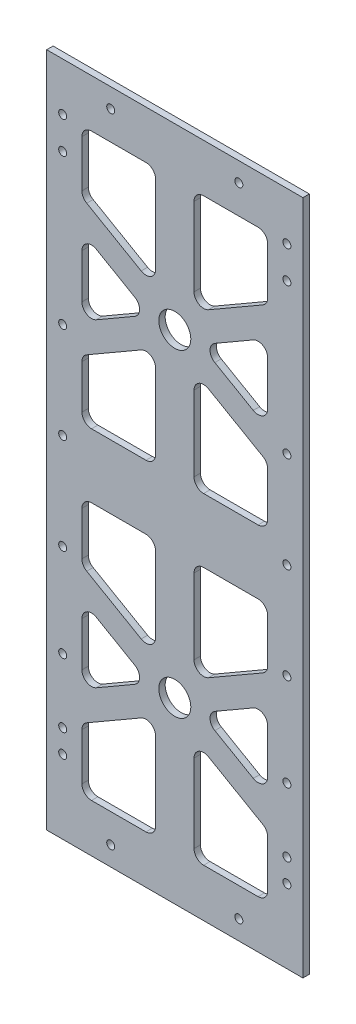
SolidWorks part; units mm, degrees
material "6061-T6 (SS)"
ref_plane "Front Plane" through (0, 0, 0) normal (0, 0, 1) x (1, 0, 0)
ref_plane "Top Plane" through (0, 0, 0) normal (0, 1, 0) x (1, 0, 0)
ref_plane "Right Plane" through (0, 0, 0) normal (1, 0, 0) x (0, 0, -1)
sketch "Sketch1" plane through (0, 0, 0) normal (0, 0, 1) x (1, 0, 0)
  line L1 (0, 0) -> (88, 0)
  line L2 (0, 0) -> (0, 211)
  line L3 (0, 211) -> (88, 211)
  line L4 (88, 0) -> (88, 211)
  dimension "D1" = 88
  dimension "D2" = 211
extrude "Boss-Extrude1" add sketch "Sketch1" along normal blind 2
sketch "Sketch2" plane through (0, 0, 2) normal (0, 0, 1) x (1, 0, 0)
  line L0 (0, 105.5) -> (88, 105.5) construction
  line L1 (0, 211) -> (0, 0) construction
  line L2 (88, 0) -> (88, 211) construction
  line L3 (44, 211) -> (44, 0) construction
  line L4 (88, 211) -> (0, 211) construction
  line L5 (0, 0) -> (88, 0) construction
  line L6 (0, 155.25) -> (88, 155.25) construction
  line L7 (0, 55.75) -> (88, 55.75) construction
  dimension "D1" = 55.75
  dimension "D2" = 55.75
sketch "Sketch3" plane through (0, 0, 2) normal (0, 0, 1) x (1, 0, 0)
  line L0 (0, 155.25) -> (88, 155.25) construction
  line L1 (38, 196) -> (38, 115.5)
  line L2 (0, 211) -> (0, 0) construction
  line L3 (15, 196) -> (73, 196)
  line L4 (15, 196) -> (15, 115.5)
  line L5 (15, 115.5) -> (73, 115.5)
  line L6 (73, 196) -> (73, 115.5)
  line L7 (88, 211) -> (0, 211) construction
  line L8 (88, 0) -> (88, 211) construction
  line L9 (0, 105.5) -> (88, 105.5) construction
  line L13 (73, 171.9932) -> (15, 138.5068) construction
  line L14 (15, 171.9932) -> (73, 138.5068) construction
  line L15 (73, 176.612) -> (15, 143.1256)
  line L16 (73, 167.3744) -> (15, 133.888)
  line L17 (15, 176.612) -> (73, 143.1256)
  line L18 (15, 167.3744) -> (73, 133.888)
  line L19 (50, 196) -> (50, 115.5)
  circle A0 centre (44, 155.25) radius 5
  dimension "D1" = 10
  dimension "D3" = 15
  dimension "D4" = 15
  dimension "D5" = 15
  dimension "D6" = 10
  dimension "D9" = 30
  dimension "D10" = 30
  dimension "D11" = 8
  dimension "D12" = 4
  dimension "D13" = 4
  dimension "D14" = 8
ref_plane "Plane1" through (0, 105.5, 0) normal (0, 1, 0) x (1, 0, 0)
extrude "Cut-Extrude2" cut sketch "Sketch3" against normal blind 2
sketch "Sketch4" plane through (0, 0, 2) normal (0, 0, 1) x (1, 0, 0)
  line L0 (0, 155.25) -> (88, 155.25) construction
  circle A0 centre (44, 155.25) radius 5
  dimension "D1" = 10
extrude "Cut-Extrude3" cut sketch "Sketch4" against normal through all
mirror "Mirror2" about plane through (0, 105.5, 0) normal (0, 1, 0) of "Cut-Extrude2", "Cut-Extrude3"
fillet "Fillet2" radius 3 44 edges at (73, 67.8744, 1) (73, 43.6256, 1) (52, 55.75, 1) (15, 15, 1) (15, 34.388, 1) (15, 143.1256, 1) (15, 167.3744, 1) (36, 155.25, 1) (15, 115.5, 1) (15, 133.888, 1) (73, 196, 1) (73, 115.5, 1) (73, 133.888, 1) (15, 196, 1) (15, 176.612, 1) (73, 167.3744, 1) (73, 143.1256, 1) (52, 155.25, 1) (73, 95.5, 1) (73, 77.112, 1) (73, 34.388, 1) (73, 15, 1) (15, 77.112, 1) (15, 95.5, 1) (15, 43.6256, 1) (15, 67.8744, 1) (36, 55.75, 1) (73, 176.612, 1) (50, 15, 1) (38, 15, 1) (38, 47.6671, 1) (50, 47.6671, 1) (38, 63.8329, 1) (38, 95.5, 1) (50, 63.8329, 1) (50, 95.5, 1) (38, 115.5, 1) (38, 147.1671, 1) (50, 147.1671, 1) (50, 115.5, 1) (38, 196, 1) (38, 163.3329, 1) (50, 163.3329, 1) (50, 196, 1)
sketch "Sketch23" plane through (0, 0, 2) normal (0, 0, 1) x (1, 0, 0)
  line L2 (88, 211) -> (88, 0)
  line L3 (86, 211) -> (86, 0)
  line L4 (86, 211) -> (88, 211)
  line L5 (86, 0) -> (88, 0)
  line L6 (2.1504, 211) -> (2.1504, 0)
  line L7 (2.1504, 211) -> (0, 211)
  line L8 (0, 211) -> (0, 0)
  line L9 (2.1504, 0) -> (0, 0)
  dimension "D1" = 2
extrude "Cut-Extrude5" cut sketch "Sketch23" against normal blind 10 contours L5 L2 L4 L3 | L6 L9 L8 L7
sketch "Sketch29" plane through (0, 0, 0) normal (0, 0, -1) x (-1, 0, 0)
  line L0 (-44, 0) -> (-44, 211)
  line L4 (-86, 105.5) -> (-2.1504, 105.5)
  line L5 (-86, 0) -> (-86, 211) construction
  line L6 (-2.1504, 0) -> (-2.1504, 211) construction
  line L16 (-4, 211) -> (1.9115, 211)
  line L17 (-4, 211) -> (-4, 0)
  line L18 (-4, 0) -> (1.9115, 0)
  line L19 (1.9115, 211) -> (1.9115, 0)
  line L20 (-84, 0) -> (-88.0365, 0)
  line L21 (-84, 0) -> (-84, 211)
  line L22 (-84, 211) -> (-88.0365, 211)
  line L23 (-88.0365, 0) -> (-88.0365, 211)
  point P0 (-44, 155.25)
  point P1 (-44, 217.1483)
  point P3 (-4, 155.25)
  point P4 (-4, 217.1483)
  point P5 (-84, 155.25)
  point P6 (-84, 217.1483)
  point P8 (-4, 105.5)
  point P22 (-84, 105.5)
  point P23 (-44, 105.5)
extrude "Cut-Extrude10" cut sketch "Sketch29" against normal blind 2
hole_wizard "M3x0.5 Tapped Hole1" positions "Sketch31" profile "Sketch32" tap size "M3x0.5" standard "ANSI Metric"
sketch "Sketch31" plane through (0, 0, 2) normal (0, 0, 1) x (1, 0, 0)
  line L0 (44, 211) -> (44, 0) construction
  line L1 (84, 211) -> (4, 211) construction
  line L2 (4, 0) -> (84, 0) construction
  line L3 (9, 186) -> (44, 211) construction
  line L4 (44, 211) -> (79, 186) construction
  line L5 (4, 0) -> (84, 0) construction
  line L6 (84, 211) -> (4, 211) construction
  point P0 (9, 186)
  point P2 (9, 139.2)
  point P4 (9, 109.2)
  point P6 (9, 79.2)
  point P8 (9, 50.2)
  point P10 (9, 30.2)
  point P20 (79, 186)
  point P22 (79, 139.2)
  point P24 (79, 109.2)
  point P26 (79, 79.2)
  point P28 (79, 50.2)
  point P30 (79, 30.2)
  point P51 (24, 6)
  point P53 (64, 6)
  point P59 (24, 205)
  point P61 (64, 205)
  point P70 (9, 196)
  point P72 (79, 196)
  point P76 (9, 23)
  point P78 (79, 23)
  dimension "D1" = 70
  dimension "D2" = 25
  dimension "D3" = 46.8
  dimension "D4" = 30
  dimension "D5" = 30
  dimension "D6" = 20
  dimension "D7" = 29
  dimension "D8" = 6
  dimension "D9" = 40
  dimension "D10" = 20
  dimension "D11" = 6
  dimension "D12" = 15
  dimension "D13" = 70
  dimension "D14" = 35
  dimension "D15" = 23
sketch "Sketch32" plane through (9, 186, 2) normal (1, 0, 0) x (0, -1, 0)
  line L0 (0, 0) -> (0, 10.7511)
  line L1 (0, 10.7511) -> (1.25, 10)
  line L2 (1.25, 10) -> (1.25, 0)
  line L5 (1.25, 0) -> (0, 0)
  line L10 (0, 10.7511) -> (-1.25, 10) construction
  line L11 (0, -6.35) -> (0, 107.95) construction
  dimension "Tap Drill Dia." = 2.5
  dimension "Tap Drill Depth" = 10
  dimension "Drill Angle" = 118
equation "\"stack_house_hole_distance\"=15"
equation "\"battery_top_clearance\"=15"
equation "\"coils_top_clearance\"=10"
